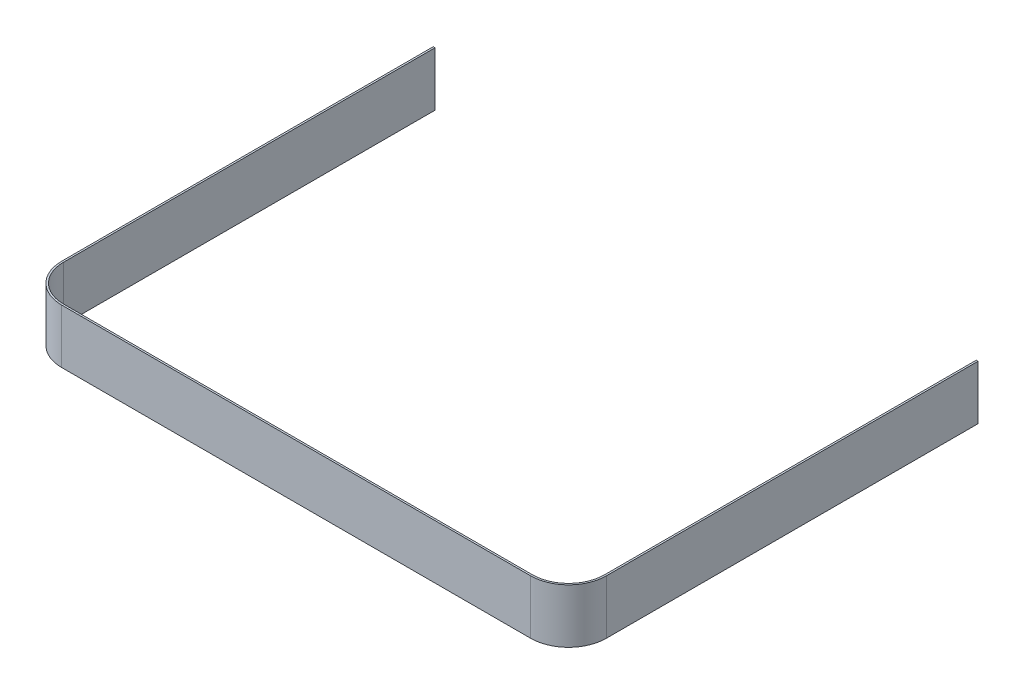
SolidWorks part; units mm, degrees
ref_plane "Ebene vorne" through (0, 0, 0) normal (0, 0, 1) x (1, 0, 0)
ref_plane "Ebene oben" through (0, 0, 0) normal (0, 1, 0) x (1, 0, 0)
ref_plane "Ebene rechts" through (0, 0, 0) normal (1, 0, 0) x (0, 0, -1)
sketch "Skizze1" plane through (0, 0, 0) normal (0, -1, 0) x (1, 0, 0)
  line L0 (0, 75) -> (130, 75)
  line L1 (150, -150) -> (150, -151)
  line L2 (150, 55) -> (150, -150)
  arc A0 (130, 75) -> (150, 55) centre (130, 55) cw
  dimension "D1" = 1
extrude "Linear-Austragen-Dünn1" add sketch "Skizze1" against normal blind 30 thin thin type one direction reverse wall 1
mirror "Spiegeln1" about plane through (0, 30, 75) normal (1, 0, 0) of "Linear-Austragen-Dünn1"
